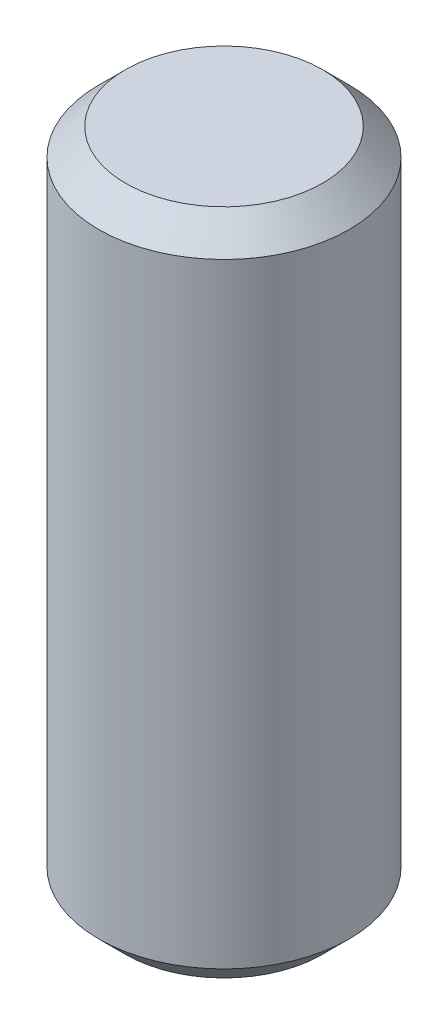
SolidWorks part; units mm, degrees
ref_plane "Front Plane" through (0, 0, 0) normal (0, 0, 1) x (1, 0, 0)
ref_plane "Top Plane" through (0, 0, 0) normal (0, 1, 0) x (1, 0, 0)
ref_plane "Right Plane" through (0, 0, 0) normal (1, 0, 0) x (0, 0, -1)
sketch "Sketch1" plane through (0, 0, 0) normal (0, 0, 1) x (1, 0, 0)
  line L0 (0, 0.7605) -> (0, -0.7605) construction
  line L1 (0, -3.175) -> (1.1906, -3.175)
  line L2 (1.1906, -3.175) -> (1.1906, 3.175)
  line L3 (1.1906, 3.175) -> (0, 3.175)
  line L4 (0, 3.175) -> (0, -3.175)
  point P7 (0, 0)
  dimension "D1" = 2.3813
  dimension "D2" = 6.35
revolve "Revolve1" add sketch "Sketch1" angle 360 about L0
chamfer "Chamfer1" distance 0.254 angle 45 2 edges at (0, -3.175, 1.1906) (0, 3.175, 1.1906)
